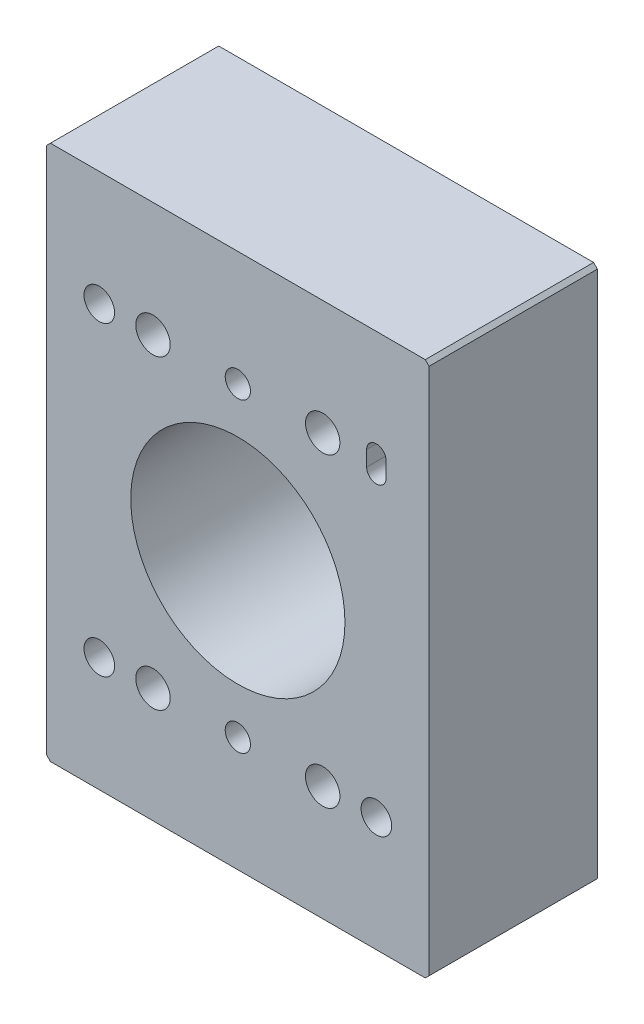
SolidWorks part; units mm, degrees
ref_plane "Front Plane" through (0, 0, 0) normal (0, 0, 1) x (1, 0, 0)
ref_plane "Top Plane" through (0, 0, 0) normal (0, 1, 0) x (1, 0, 0)
ref_plane "Right Plane" through (0, 0, 0) normal (1, 0, 0) x (0, 0, -1)
sketch "Sketch1" plane through (0, 0, 0) normal (0, 0, 1) x (1, 0, 0)
  line L1 (-19.7216, 14.4559) -> (30.2784, 14.4559)
  line L2 (-19.7216, 14.4559) -> (-19.7216, -55.5441)
  line L3 (-19.7216, -55.5441) -> (30.2784, -55.5441)
  line L4 (30.2784, 14.4559) -> (30.2784, -55.5441)
  line L6 (22.1154, 0.4559) -> (22.1154, -1.5441)
  line L8 (24.6577, 0.4559) -> (24.6577, -1.5441)
  circle A0 centre (5.2784, -20.5441) radius 14
  circle A1 centre (-12.8297, -0.5441) radius 2
  circle A2 centre (-5.8135, -0.5441) radius 2.25
  circle A3 centre (-5.8135, -40.5441) radius 2.25
  circle A4 centre (-12.8297, -40.5441) radius 2
  circle A5 centre (23.3865, -40.5441) radius 2
  circle A6 centre (16.3703, -40.5441) radius 2.25
  arc A7 (24.6577, 0.4559) -> (22.1154, 0.4559) centre (23.3865, 0.4559) ccw
  circle A8 centre (16.3703, -0.5441) radius 2.25
  arc A9 (22.1154, -1.5441) -> (24.6577, -1.5441) centre (23.3865, -1.5441) ccw
  point P6 (5.2784, 14.4559)
  point P7 (5.2784, -55.5441)
  point P8 (-19.7216, -20.5441)
  point P9 (30.2784, -20.5441)
  point P25 (0, 0)
  dimension "D3" = 28
  dimension "D4" = 4
  dimension "D5" = 4.5
  dimension "D6" = 2
  dimension "D1" = 50
  dimension "D2" = 70
  dimension "D7" = 15
  dimension "D8" = 15
extrude "Boss-Extrude1" add sketch "Sketch1" along normal blind 22
hole_wizard "M4 Tapped Hole1" positions "Sketch2" profile "Sketch3" tap size "M4" standard "ISO" end condition through all
sketch "Sketch2" plane through (0, 0, 22) normal (0, 0, 1) x (1, 0, 0)
  line L0 (-19.7216, -55.5441) -> (30.2784, -55.5441) construction
  point P0 (5.2784, -0.5441)
  point P2 (5.2784, -40.5441)
  dimension "D1" = 40
  dimension "D2" = 55
cosmetic thread "Hole Thread1" parameters "D2"=4
cosmetic thread "Hole Thread2" parameters "D2"=4
sketch "Sketch3" plane through (5.2784, -0.5441, 22) normal (1, 0, 0) x (0, -1, 0)
  line L0 (0, 0) -> (0, 22)
  line L1 (0, 22) -> (1.65, 22)
  line L2 (1.65, 22) -> (1.65, 0)
  line L5 (1.65, 0) -> (0, 0)
  line L11 (0, -6.35) -> (0, 107.95) construction
  dimension "Thru Tap Drill Dia." = 3.3
  dimension "Thru Tap Drill Depth" = 22
chamfer "Chamfer1" distance 0.5 angle 45 4 edges at (-19.7216, -55.5441, 11) (30.2784, -55.5441, 11) (30.2784, 14.4559, 11) (-19.7216, 14.4559, 11)
